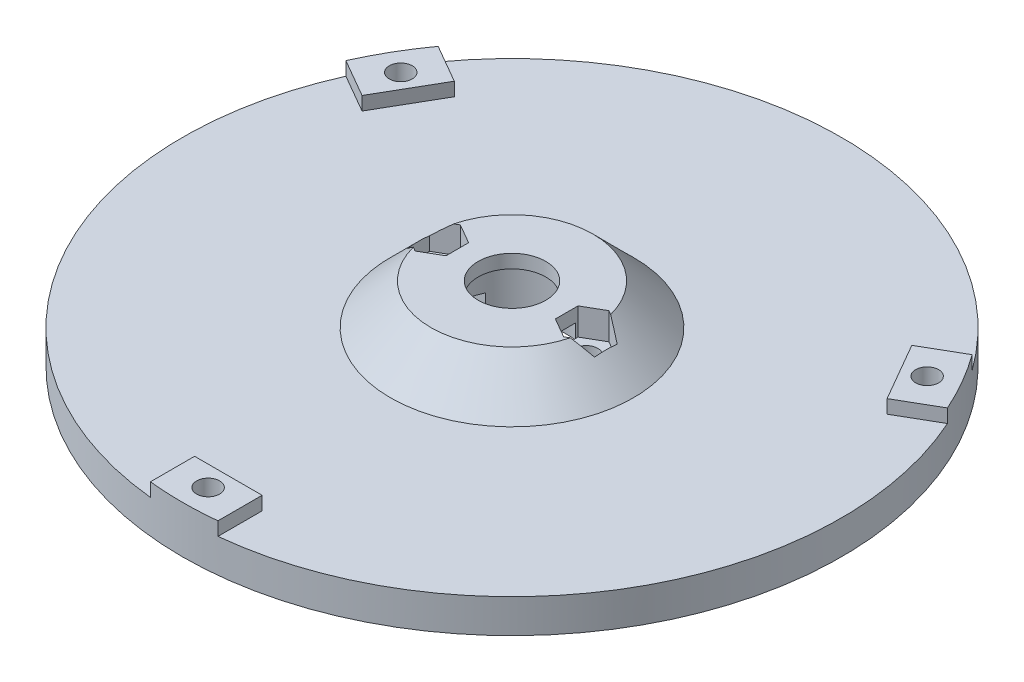
SolidWorks part; units mm, degrees
material "PLA"
ref_plane "Alzado" through (0, 0, 0) normal (0, 0, 1) x (1, 0, 0)
ref_plane "Planta" through (0, 0, 0) normal (0, 1, 0) x (1, 0, 0)
ref_plane "Vista lateral" through (0, 0, 0) normal (1, 0, 0) x (0, 0, -1)
sketch "Croquis1" plane through (0, 0, 0) normal (0, 0, 1) x (1, 0, 0)
  line L0 (5, 11) -> (12, 11)
  line L1 (12, 11) -> (18, 5)
  line L2 (18, 5) -> (48.8, 5)
  line L3 (48.8, 5) -> (48.8, 0)
  line L4 (48.8, 0) -> (8.2, 0)
  line L5 (8.2, 0) -> (8.2, 9)
  line L6 (8.2, 9) -> (5, 9)
  line L7 (5, 9) -> (5, 11)
  line L8 (0, 21.1097) -> (0, -10.7898) construction
  dimension "D1" = 5
  dimension "D2" = 48.8
  dimension "D3" = 45
  dimension "D4" = 12
  dimension "D5" = 5
  dimension "D6" = 2
  dimension "D7" = 9
  dimension "D8" = 8.2
revolve "Revolución1" add sketch "Croquis1" angle 360 about L8
sketch "Croquis2" plane through (0, 0, 0) normal (0, -1, 0) x (1, 0, 0)
  line L1 (15.3, -3.5) -> (-15.3, -3.5)
  line L2 (15.3, -3.5) -> (15.3, 3.5)
  line L3 (15.3, 3.5) -> (-15.3, 3.5)
  line L4 (-15.3, -3.5) -> (-15.3, 3.5)
  line L5 (15.3, -3.5) -> (-15.3, 3.5) construction
  line L6 (15.3, 3.5) -> (-15.3, -3.5) construction
  point P0 (0, 0)
  dimension "D1" = 30.6
  dimension "D2" = 7
extrude "Cortar-Extruir1" cut sketch "Croquis2" against normal blind 4
sketch "Croquis3" plane through (0, 4, 0) normal (0, -1, 0) x (1, 0, 0)
  line L0 (-11, 0) -> (11, 0) construction
  circle A0 centre (-11, 0) radius 1.7
  circle A1 centre (11, 0) radius 1.7
  point P5 (0, 0)
  dimension "D1" = 3.4
  dimension "D2" = 22
extrude "Cortar-Extruir2" cut sketch "Croquis3" against normal blind 13
sketch "Croquis4" plane through (0, 11, 0) normal (0, 1, 0) x (1, 0, 0)
  line L0 (0, 8.4706) -> (0, -7.057) construction
  line L1 (-11, 3.35) -> (-13.9012, 1.675)
  line L2 (-13.9012, 1.675) -> (-13.9012, -1.675)
  line L3 (-13.9012, -1.675) -> (-11, -3.35)
  line L4 (-11, -3.35) -> (-8.0988, -1.675)
  line L5 (-8.0988, -1.675) -> (-8.0988, 1.675)
  line L6 (-8.0988, 1.675) -> (-11, 3.35)
  line L7 (11, 3.35) -> (8.0988, 1.675)
  line L8 (8.0988, 1.675) -> (8.0988, -1.675)
  line L9 (8.0988, -1.675) -> (11, -3.35)
  line L10 (11, -3.35) -> (13.9012, -1.675)
  line L11 (13.9012, -1.675) -> (13.9012, 1.675)
  line L12 (13.9012, 1.675) -> (11, 3.35)
  circle A0 centre (-11, 0) radius 3.35 construction
  circle A1 centre (11, 0) radius 3.35 construction
  dimension "D1" = 6.7
extrude "Cortar-Extruir3" cut sketch "Croquis4" against normal blind 4
sketch "Croquis5" plane through (0, 5, 0) normal (0, 1, 0) x (1, 0, 0)
  line L1 (5, -42) -> (-5, -42)
  line L2 (5, -42) -> (5, -48.5432)
  line L4 (-5, -42) -> (-5, -48.5432)
  arc A0 (-5, -48.5432) -> (5, -48.5432) centre (0, 0) ccw
  circle A1 centre (0, 0) radius 48.8 construction
  point P10 (0, -42)
  dimension "D1" = 10
  dimension "D2" = 42
extrude "Saliente-Extruir1" add sketch "Croquis5" along normal blind 2
sketch "Croquis6" plane through (0, 7, 0) normal (0, 1, 0) x (1, 0, 0)
  circle A0 centre (0, -45) radius 1.7
  dimension "D2" = 3.4
  dimension "D1" = 45
extrude "Cortar-Extruir4" cut sketch "Croquis6" against normal blind 9
sketch "Croquis7" plane through (0, 0, 0) normal (0, -1, 0) x (1, 0, 0)
  circle A0 centre (0, 45) radius 2.95
  dimension "D1" = 5.9
extrude "Cortar-Extruir5" cut sketch "Croquis7" against normal blind 3
pattern_circular "MatrizC1" count 3 over 360 about axis through (0, 0, 0) along (0, 1, 0) of "Saliente-Extruir1", "Cortar-Extruir4", "Cortar-Extruir5"
